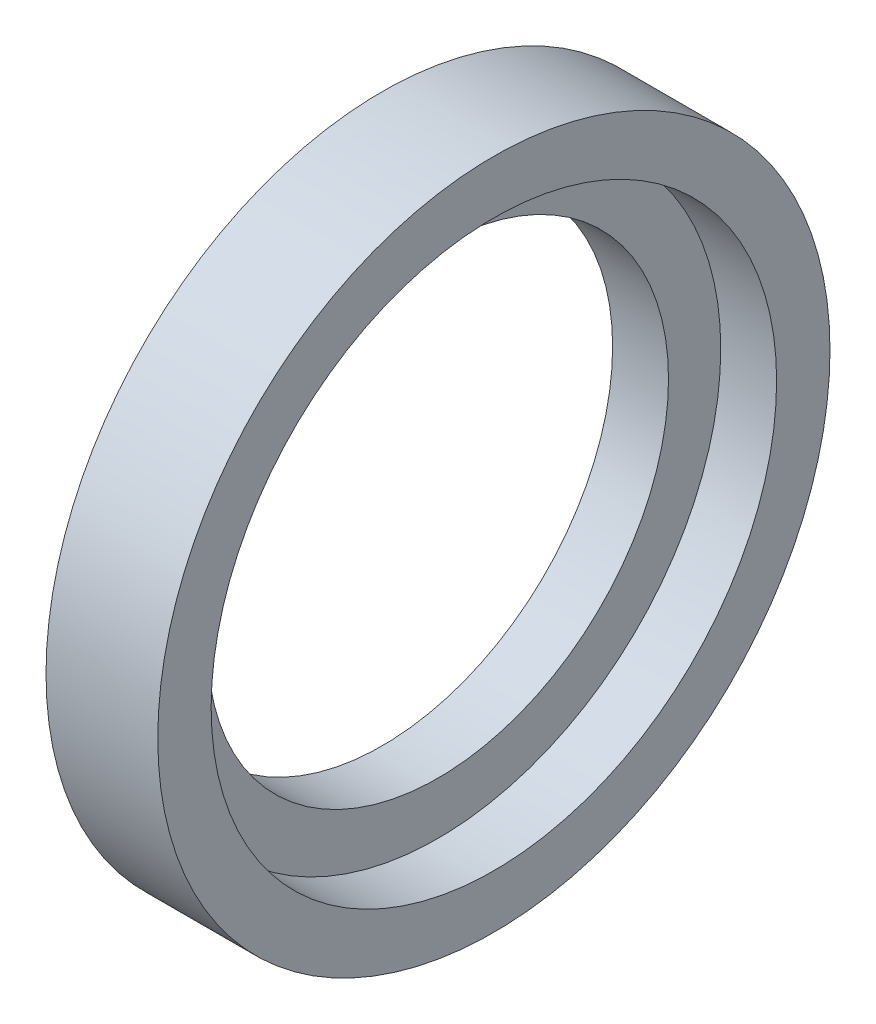
SolidWorks part; units mm, degrees
ref_plane "Front Plane" through (0, 0, 0) normal (0, 0, 1) x (1, 0, 0)
ref_plane "Top Plane" through (0, 0, 0) normal (0, 1, 0) x (1, 0, 0)
ref_plane "Right Plane" through (0, 0, 0) normal (1, 0, 0) x (0, 0, -1)
sketch "Sketch1" plane through (0, 0, 0) normal (1, 0, 0) x (0, 0, -1)
  circle A0 centre (0, 0) radius 20.625
  circle A1 centre (0, 0) radius 30.075
extrude "Boss-Extrude1" add sketch "Sketch1" along normal blind 10
sketch "Sketch2" plane through (10, 0, 0) normal (1, 0, 0) x (0, 0, -1)
  circle A0 centre (0, 0) radius 25.3
extrude "Cut-Extrude1" cut sketch "Sketch2" against normal blind 5
